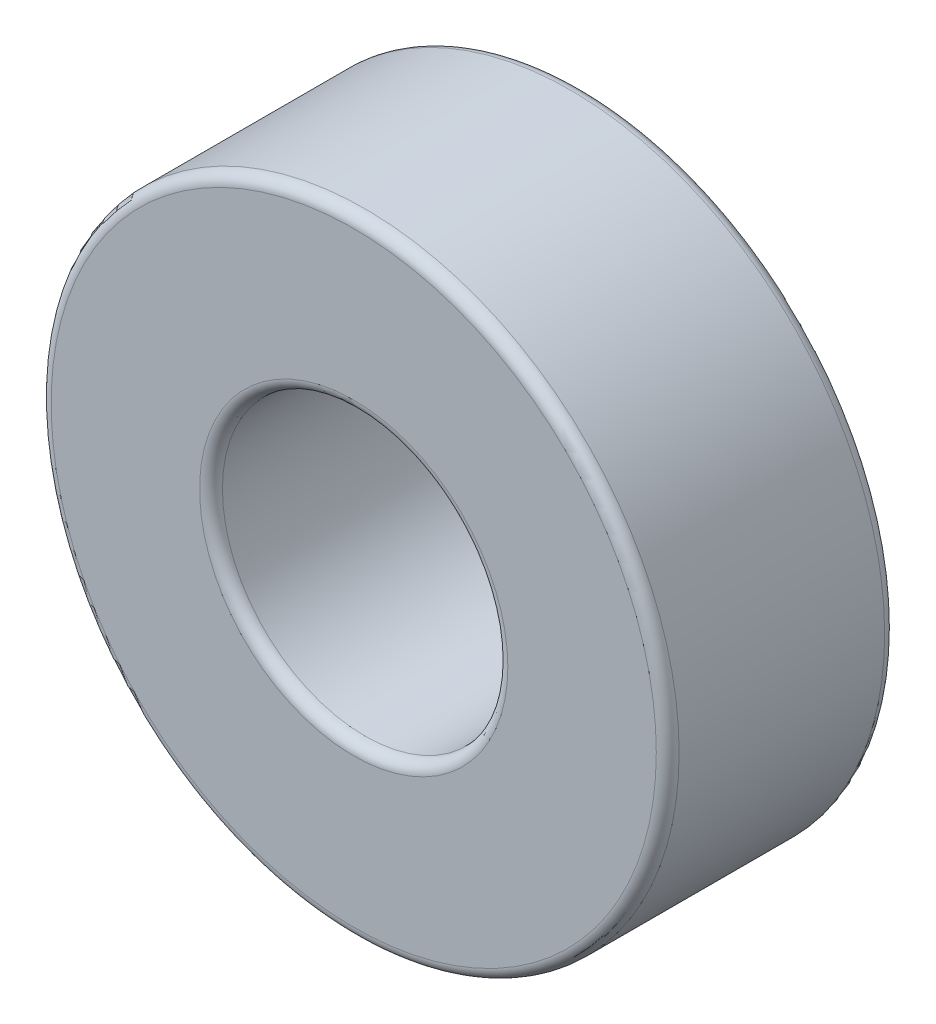
SolidWorks part; units mm, degrees
material "Stainless Steel (ferritic)"
ref_plane "Front Plane" through (0, 0, 0) normal (0, 0, 1) x (1, 0, 0)
ref_plane "Top Plane" through (0, 0, 0) normal (0, 1, 0) x (1, 0, 0)
ref_plane "Right Plane" through (0, 0, 0) normal (1, 0, 0) x (0, 0, -1)
sketch "Sketch1" plane through (0, 0, 0) normal (0, 0, 1) x (1, 0, 0)
  circle A0 centre (0, 0) radius 2.5
  circle A1 centre (0, 0) radius 5.5
  dimension "D1" = 5
  dimension "D2" = 11
extrude "Boss-Extrude1" add sketch "Sketch1" along normal blind 4
fillet "Fillet1" radius 0.2 4 edges at (2.5, 0, 0) (5.5, 0, 0) (5.5, 0, 4) (2.5, 0, 4)
